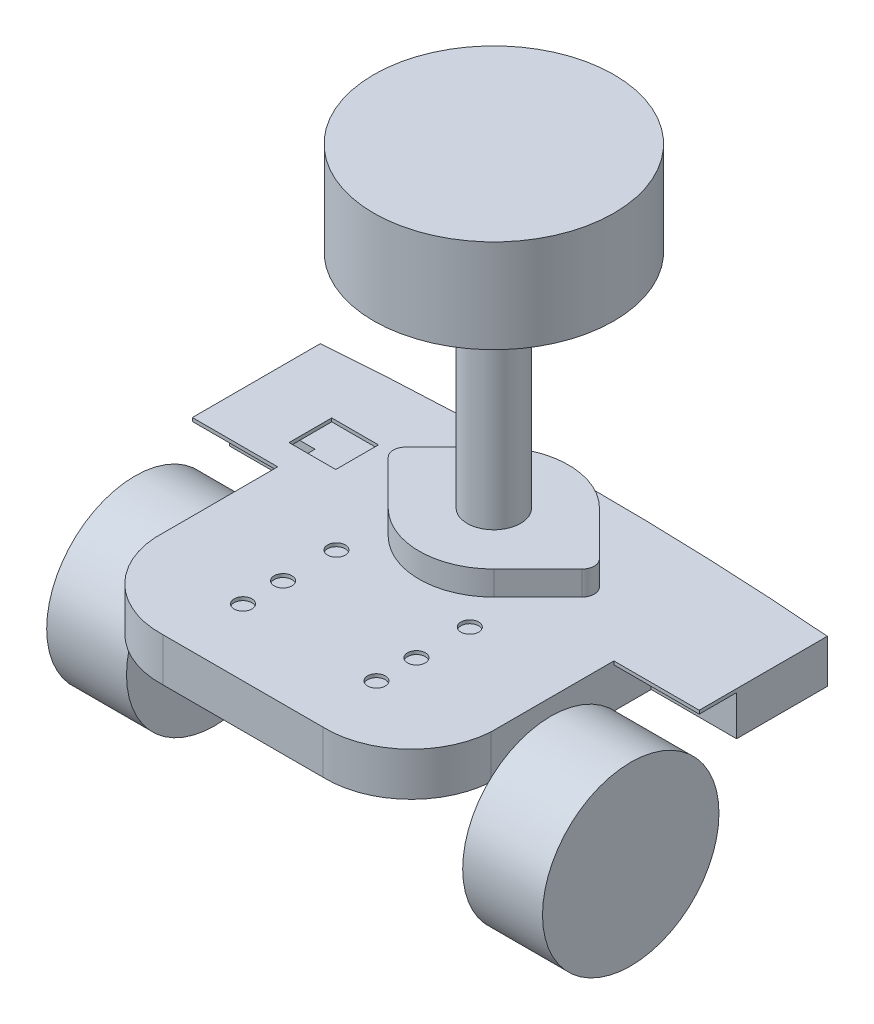
SolidWorks part; units mm, degrees
ref_plane "Front Plane" through (0, 0, 0) normal (0, 0, 1) x (1, 0, 0)
ref_plane "Top Plane" through (0, 0, 0) normal (0, 1, 0) x (1, 0, 0)
ref_plane "Right Plane" through (0, 0, 0) normal (1, 0, 0) x (0, 0, -1)
sketch "Sketch1" plane through (0, 0, 0) normal (0, 1, 0) x (1, 0, 0)
  line L0 (0, 0) -> (0, 125.2845) construction
  line L1 (19.05, 0) -> (-19.05, 0)
  line L2 (-40.005, 19.05) -> (-40.005, 48.26)
  line L3 (-40.005, 48.26) -> (-60.325, 48.26)
  line L4 (-60.325, 48.26) -> (-60.325, 78.74)
  line L5 (-60.325, 78.74) -> (60.325, 78.74)
  line L6 (60.325, 48.26) -> (60.325, 78.74)
  line L7 (40.005, 48.26) -> (60.325, 48.26)
  line L8 (40.005, 19.05) -> (40.005, 48.26)
  arc A0 (-40.005, 19.05) -> (-19.05, 0) centre (-19.724, 20.3088) ccw
  arc A1 (40.005, 19.05) -> (19.05, 0) centre (19.724, 20.3088) cw
  point P14 (0, 78.74)
  dimension "D4" = 20.32
  dimension "D1" = 120.65
  dimension "D2" = 80.01
  dimension "D3" = 38.1
  dimension "D5" = 19.05
  dimension "D6" = 48.26
  dimension "D7" = 78.74
extrude "Extrude1" add sketch "Sketch1" along normal blind 0.8128
sketch "Sketch3" plane through (0, 0.8128, 0) normal (0, 1, 0) x (-1, 0, 0)
  line L0 (0, -78.74) -> (0, 0) construction
  line L1 (-60.325, -78.74) -> (60.325, -78.74) construction
  line L2 (-21, -59.69) -> (21, -59.69) construction
  circle A0 centre (0, -59.69) radius 17.78
  circle A1 centre (21, -59.69) radius 1.651
  circle A2 centre (-21, -59.69) radius 1.651
  dimension "D1" = 35.56
  dimension "D3" = 42
  dimension "D4" = 3.302
  dimension "D2" = 19.05
extrude "Extrude2" cut sketch "Sketch3" against normal through all
sketch "Sketch4" plane through (0, 0.8128, 0) normal (0, 1, 0) x (-1, 0, 0)
  line L0 (38.1, -78.74) -> (38.1, -47.0431) construction
  line L1 (-60.325, -78.74) -> (60.325, -78.74) construction
  line L2 (60.325, -78.74) -> (60.325, -48.26) construction
  line L3 (38.1, -59.69) -> (21, -59.69) construction
  line L4 (43.6562, -54.61) -> (32.5438, -54.61)
  line L5 (43.6562, -54.61) -> (43.6562, -64.77)
  line L6 (43.6562, -64.77) -> (32.5438, -64.77)
  line L7 (32.5438, -54.61) -> (32.5438, -64.77)
  line L8 (43.6562, -54.61) -> (32.5438, -64.77) construction
  line L9 (43.6562, -64.77) -> (32.5438, -54.61) construction
  point P6 (38.1, -59.69)
  dimension "D1" = 22.225
  dimension "D2" = 11.1125
  dimension "D3" = 10.16
extrude "Cut-Extrude1" cut sketch "Sketch4" against normal through all
sketch "Sketch5" plane through (0, 0.8128, 0) normal (0, 1, 0) x (-1, 0, 0)
  line L0 (15.875, -78.74) -> (15.875, 0) construction
  line L1 (0, -78.74) -> (0, 0) construction
  line L2 (-60.325, -78.74) -> (60.325, -78.74) construction
  line L3 (19.05, 0) -> (-19.05, 0) construction
  circle A0 centre (15.875, -38.1) radius 2.1082
  circle A1 centre (15.875, -25.4) radius 2.1082
  circle A2 centre (15.875, -15.875) radius 2.1082
  circle A3 centre (-15.875, -15.875) radius 2.1082
  circle A4 centre (-15.875, -25.4) radius 2.1082
  circle A5 centre (-15.875, -38.1) radius 2.1082
  dimension "D2" = 4.2164
  dimension "D3" = 12.7
  dimension "D4" = 9.525
  dimension "D5" = 15.875
  dimension "D1" = 15.875
extrude "Extrude3" cut sketch "Sketch5" against normal through all
sketch "Sketch6" plane through (0, 0.8128, 0) normal (0, 1, 0) x (1, 0, 0)
  line L0 (-60.325, 78.74) -> (60.325, 78.74)
  arc A0 (-60.325, 78.74) -> (60.325, 78.74) centre (0, -680.8684) cw
  dimension "D1" = 762
extrude "Extrude5" add sketch "Sketch6" against normal through all
sketch "Sketch7" plane through (0, 0, 0) normal (0, -1, 0) x (1, 0, 0)
  line L7 (-60.325, -78.74) -> (-60.325, -57.15)
  line L8 (-60.325, -78.74) -> (-60.325, -48.26) construction
  line L9 (-60.325, -57.15) -> (-40.005, -57.15)
  line L10 (-60.325, -48.26) -> (-40.005, -48.26) construction
  line L11 (0, -81.1316) -> (0, 0) construction
  line L12 (60.325, -57.15) -> (40.005, -57.15)
  line L13 (60.325, -78.74) -> (60.325, -57.15)
  line L14 (-40.005, -19.05) -> (-40.005, -48.26)
  line L15 (-40.005, -48.26) -> (-60.325, -48.26)
  line L16 (-60.325, -48.26) -> (-60.325, -78.74)
  line L17 (60.325, -78.74) -> (60.325, -48.26)
  line L18 (60.325, -48.26) -> (40.005, -48.26)
  line L19 (40.005, -48.26) -> (40.005, -19.05)
  line L20 (19.05, 0) -> (-19.05, 0)
  line L21 (-40.005, -19.05) -> (-40.005, -57.15)
  line L26 (40.005, -57.15) -> (40.005, -19.05)
  line L27 (19.05, 0) -> (-19.05, 0)
  arc A6 (-19.05, 0) -> (-40.005, -19.05) centre (-19.724, -20.3088) ccw
  arc A7 (-60.325, -78.74) -> (60.325, -78.74) centre (0, 680.8684) ccw
  arc A8 (40.005, -19.05) -> (19.05, 0) centre (19.724, -20.3088) ccw
  arc A9 (-19.05, 0) -> (-40.005, -19.05) centre (-19.724, -20.3088) ccw
  arc A10 (-60.325, -78.74) -> (60.325, -78.74) centre (0, 680.8684) ccw
  arc A11 (40.005, -19.05) -> (19.05, 0) centre (19.724, -20.3088) ccw
  dimension "D2" = 8.89
  dimension "D1" = 0
extrude "Extrude6" add sketch "Sketch7" along normal blind 9.525
sketch "Sketch8" plane through (0, 0, 0) normal (0, 1, 0) x (1, 0, 0)
  line L0 (-23.0656, 61.7523) -> (-12.5824, 72.2523)
  line L1 (-21, 59.69) -> (0, 59.69) construction
  line L2 (0, 59.69) -> (0, 77.47) construction
  line L3 (23.0656, 61.7523) -> (12.5824, 72.2523)
  line L4 (-23.0656, 57.6277) -> (-12.5824, 47.1277)
  line L5 (23.0656, 57.6277) -> (12.5824, 47.1277)
  circle A0 centre (0, 59.69) radius 17.78
  circle A1 centre (21, 59.69) radius 2.9188
  circle A2 centre (-21, 59.69) radius 2.9188
  circle A3 centre (0, 59.69) radius 17.78 construction
  circle M1 centre (0, 59.69) radius 17.78
extrude "Extrude7" add sketch "Sketch8" along normal blind 6.604 contours A2 L4 L0 M1 | A2 | M1 | A1 L3 L5 M1 | A1
sketch "Sketch9" plane through (40.005, 0, 0) normal (1, 0, 0) x (0, 0, -1)
  line L0 (0, 0.8128) -> (0, -9.525) construction
  line L1 (19.05, 0.8128) -> (48.26, 0.8128) construction
  circle A0 centre (33.274, -24.0792) radius 21
  point P2 (0, -4.3561)
  dimension "D1" = 42
  dimension "D2" = 33.274
  dimension "D3" = 24.892
extrude "Extrude8" add sketch "Sketch9" along normal blind 19 separate body
mirror "Mirror3" about plane through (0, 0, 0) normal (1, 0, 0) of bodies 108
sketch "Sketch10" plane through (0, 6.604, 0) normal (0, 1, 0) x (-1, 0, 0)
  circle A0 centre (0, -59.69) radius 6.35
  dimension "D1" = 12.7
extrude "Extrude9" add sketch "Sketch10" along normal blind 52.832
sketch "Sketch11" plane through (0, 59.436, 0) normal (0, 1, 0) x (-1, 0, 0)
  circle A0 centre (0, -59.69) radius 28.575
  dimension "D1" = 57.15
extrude "Extrude10" add sketch "Sketch11" along normal blind 22.225 separate body
